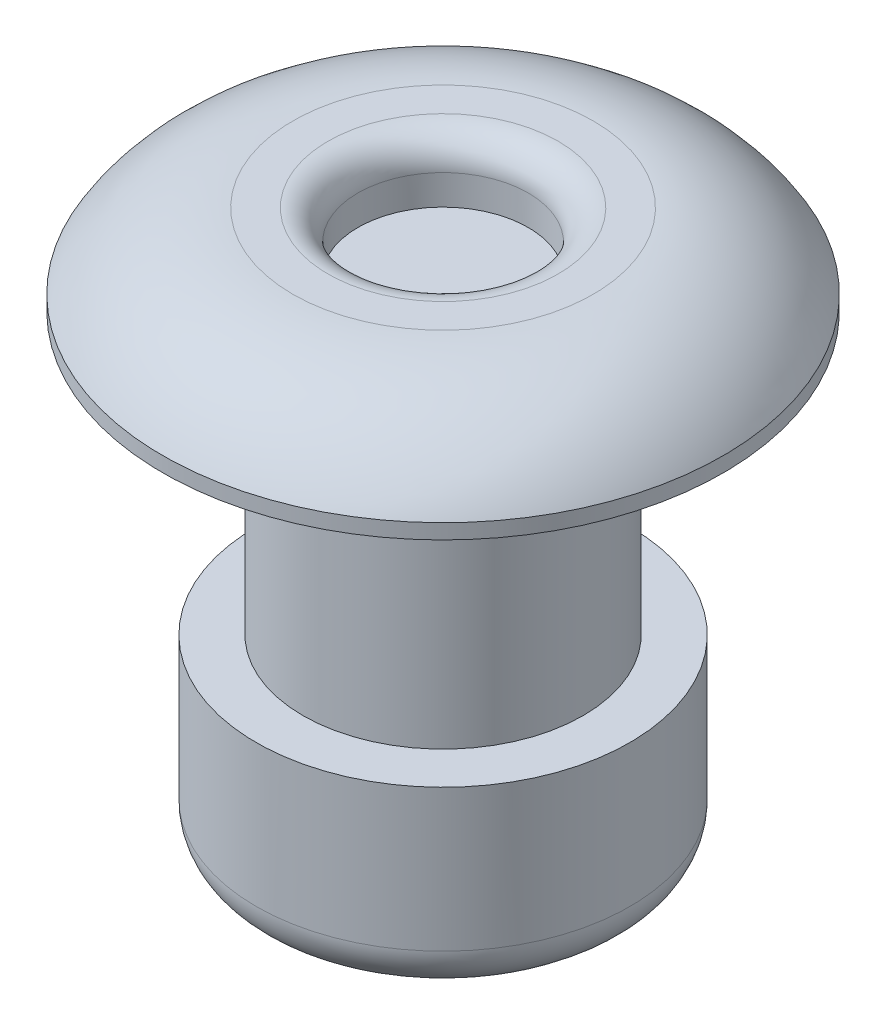
SolidWorks part; units mm, degrees
material "5052-H32"
ref_plane "Front Plane" through (0, 0, 0) normal (0, 0, 1) x (1, 0, 0)
ref_plane "Top Plane" through (0, 0, 0) normal (0, 1, 0) x (1, 0, 0)
ref_plane "Right Plane" through (0, 0, 0) normal (1, 0, 0) x (0, 0, -1)
sketch "Sketch2" plane through (0, 0, 0) normal (0, 0, 1) x (1, 0, 0)
  line L0 (0, -4.1554) -> (0, 5.0847) construction
  line L1 (0, 0) -> (-4.7625, 0)
  line L2 (0, 1.524) -> (-2.5527, 1.524)
  line L3 (0, 1.524) -> (0, 0)
  line L4 (-4.7625, 0) -> (-4.7625, 0.254)
  arc A1 (-2.5527, 1.524) -> (-4.7625, 0.254) centre (-2.5527, -1.0335) ccw
  dimension "D1" = 9.525
  dimension "D2" = 1.524
  dimension "D3" = 5.1054
  dimension "D4" = 0.254
revolve "Revolve1" add sketch "Sketch2" angle 360 about L0
sketch "Sketch3" plane through (0, 1.524, 0) normal (0, 1, 0) x (1, 0, 0)
  circle A0 centre (0, 0) radius 1.4478
  dimension "D1" = 2.8956
extrude "Cut-Extrude1" cut sketch "Sketch3" against normal blind 1.016
fillet "Fillet1" radius 0.508 1 edges at (0, 1.524, 1.4478)
sketch "Sketch4" [suppressed] plane through (0, 0, 0) normal (0, 0, 1) x (1, 0, 0)
  line L0 (0, 1.9964) -> (0, -3.1085) construction
  line L1 (0, 0) -> (-2.3812, 0)
  line L2 (-2.3812, 0) -> (-2.3812, -3.175)
  line L3 (-2.3812, -3.175) -> (-3.175, -3.175)
  line L4 (-3.175, -3.175) -> (-3.175, -6.35)
  line L5 (-3.175, -6.35) -> (-1.4478, -6.35)
  line L8 (-1.4478, -6.35) -> (-1.4478, -3.81)
  line L9 (-1.4478, -3.81) -> (0, -3.81)
  line L10 (0, -3.81) -> (0, 0)
  dimension "D1" = 3.175
  dimension "D2" = 4.7625
  dimension "D3" = 6.35
  dimension "D4" = 6.35
  dimension "D5" = 2.8956
  dimension "D6" = 2.54
revolve "Revolve2" [suppressed] add sketch "Sketch4" angle 360 about L0
fillet "Fillet2" [suppressed] radius 0.762
sketch "Sketch5" plane through (0, 0, 0) normal (0, 0, 1) x (1, 0, 0)
  line L0 (0, 0) -> (0, 3.1582) construction
  line L1 (0, 0) -> (-2.3813, 0)
  line L3 (-2.3813, 0) -> (-2.3812, -4.7625)
  line L4 (-2.3812, -4.7625) -> (-3.175, -4.7625)
  line L5 (-3.175, -4.7625) -> (-3.175, -7.9375)
  line L6 (-3.175, -7.9375) -> (-1.4478, -7.9375)
  line L7 (-1.4478, -7.9375) -> (-1.4478, -5.3975)
  line L8 (-1.4478, -5.3975) -> (0, -5.3975)
  line L9 (0, -5.3975) -> (0, 0)
  line L10 (-4.7625, 0) -> (4.7625, 0) construction
  dimension "D1" = 4.7625
  dimension "D2" = 4.7625
  dimension "D3" = 2.8956
  dimension "D4" = 2.54
  dimension "D5" = 6.35
  dimension "D6" = 3.175
revolve "Revolve3" add sketch "Sketch5" angle 360 about L0
fillet "Fillet3" radius 0.762 1 edges at (0, -7.9375, -3.175)
sketch "Sketch6" [suppressed] plane through (0, 0, 0) normal (0, 0, 1) x (1, 0, 0)
  line L0 (0, 0) -> (0, 3.2359) construction
  line L1 (0, 0) -> (-2.3813, 0)
  line L2 (-2.3813, 0) -> (-2.3812, -6.35)
  line L3 (-2.3812, -6.35) -> (-3.175, -6.35)
  line L4 (-3.175, -6.35) -> (-3.175, -9.525)
  line L5 (-3.175, -9.525) -> (-1.4478, -9.525)
  line L6 (-1.4478, -9.525) -> (-1.4478, -6.985)
  line L7 (-1.4478, -6.985) -> (0, -6.985)
  line L8 (0, -6.985) -> (0, 0)
  dimension "D1" = 4.7625
  dimension "D2" = 6.35
  dimension "D3" = 2.54
  dimension "D4" = 6.35
  dimension "D5" = 3.175
  dimension "D6" = 2.8956
revolve "Revolve4" [suppressed] add sketch "Sketch6" angle 360 about L0
fillet "Fillet4" [suppressed] radius 0.762
